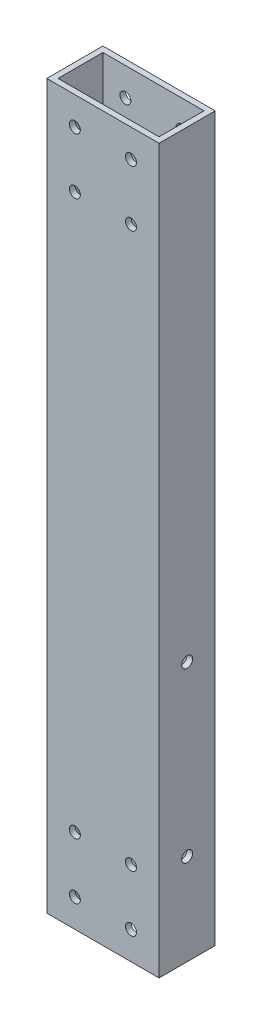
SolidWorks part; units mm, degrees
ref_plane "Front Plane" through (0, 0, 0) normal (0, 0, 1) x (1, 0, 0)
ref_plane "Top Plane" through (0, 0, 0) normal (0, 1, 0) x (1, 0, 0)
ref_plane "Right Plane" through (0, 0, 0) normal (1, 0, 0) x (0, 0, -1)
sketch "Sketch1" plane through (0, 0, 0) normal (0, 1, 0) x (1, 0, 0)
  line L1 (-25.4, -12.7) -> (25.4, -12.7)
  line L2 (-25.4, -12.7) -> (-25.4, 12.7)
  line L3 (-25.4, 12.7) -> (25.4, 12.7)
  line L4 (25.4, -12.7) -> (25.4, 12.7)
  line L5 (-25.4, -12.7) -> (25.4, 12.7) construction
  line L6 (-25.4, 12.7) -> (25.4, -12.7) construction
  point P0 (0, 0)
  dimension "D1" = 50.8
  dimension "D2" = 25.4
extrude "Extrude-Thin1" add sketch "Sketch1" along normal mid plane 327.025 thin thin type one direction reverse wall 2.54
sketch "Sketch2" [suppressed] plane through (0, 0, 12.7) normal (0, 0, 1) x (1, 0, 0)
  line L0 (25.4, -163.5125) -> (-25.4, -163.5125) construction
  circle A0 centre (0, 61.9125) radius 14.2875
  dimension "D1" = 28.575
  dimension "D2" = 225.425
extrude "Cut-Extrude1" [suppressed] cut sketch "Sketch2" against normal through all
sketch "Sketch3" plane through (0, 0, 0) normal (0, 0, 1) x (1, 0, 0)
  line L0 (25.4, -163.5125) -> (-25.4, -163.5125) construction
  line L1 (12.7, -150.8125) -> (-12.7, -150.8125) construction
  line L2 (12.7, -150.8125) -> (12.7, -125.4125) construction
  line L3 (12.7, -125.4125) -> (-12.7, -125.4125) construction
  line L4 (-12.7, -150.8125) -> (-12.7, -125.4125) construction
  line L5 (12.7, -150.8125) -> (-12.7, -125.4125) construction
  line L6 (12.7, -125.4125) -> (-12.7, -150.8125) construction
  line L7 (25.4, 163.5125) -> (-25.4, 163.5125) construction
  line L8 (12.7, 125.4125) -> (-12.7, 125.4125) construction
  line L9 (12.7, 125.4125) -> (12.7, 150.8125) construction
  line L10 (12.7, 150.8125) -> (-12.7, 150.8125) construction
  line L11 (-12.7, 125.4125) -> (-12.7, 150.8125) construction
  line L12 (12.7, 125.4125) -> (-12.7, 150.8125) construction
  line L13 (12.7, 150.8125) -> (-12.7, 125.4125) construction
  circle A0 centre (-12.7, -125.4125) radius 2.4765
  circle A1 centre (12.7, -125.4125) radius 2.4765
  circle A2 centre (12.7, -150.8125) radius 2.4765
  circle A3 centre (-12.7, -150.8125) radius 2.4765
  circle A4 centre (12.7, 150.8125) radius 2.4765
  circle A5 centre (12.7, 125.4125) radius 2.4765
  circle A6 centre (-12.7, 125.4125) radius 2.4765
  circle A7 centre (-12.7, 150.8125) radius 2.4765
  point P0 (0, -138.1125)
  point P10 (0, 138.1125)
  dimension "D3" = 4.953
  dimension "D1" = 25.4
  dimension "D2" = 25.4
  dimension "D4" = 25.4
extrude "Cut-Extrude2" cut sketch "Sketch3" against normal through all both and the other way through all
sketch "Sketch4" plane through (25.4, 0, 0) normal (1, 0, 0) x (0, 0, -1)
  circle A1 centre (0, -46.0375) radius 2.4765
  circle A2 centre (0, -46.0375) radius 2.4765
  circle A3 centre (0, -122.2375) radius 2.4765
  circle A4 centre (0, -122.2375) radius 2.4765
  dimension "D1" = 0
  dimension "D2" = 0
extrude "Cut-Extrude3" cut sketch "Sketch4" against normal blind 2.54
